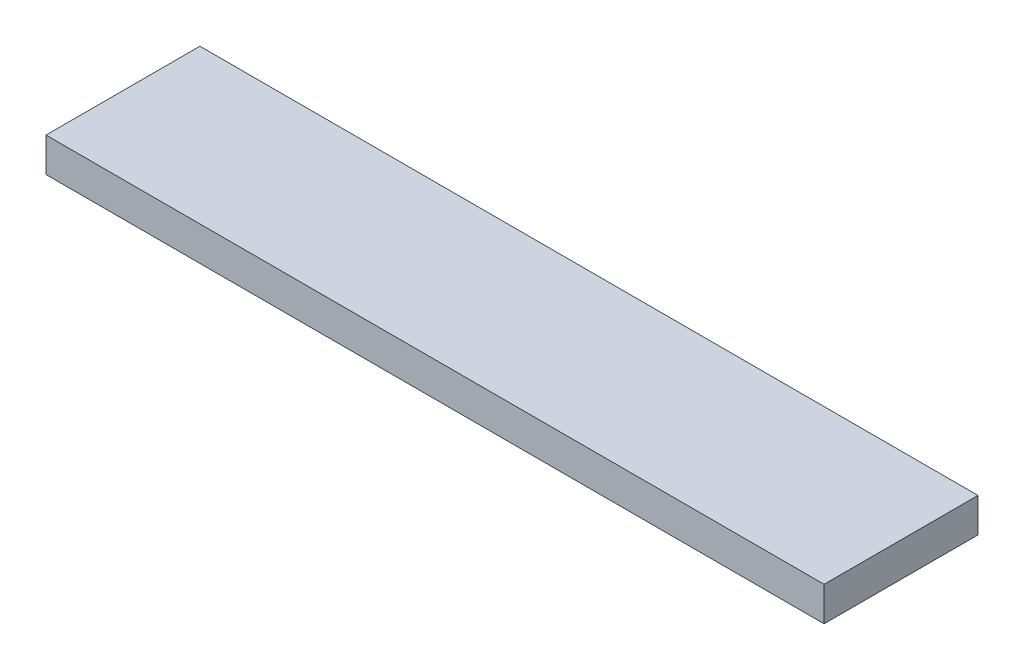
SolidWorks part; units mm, degrees
material "Polyurethane Foam Flexible"
ref_plane "Front Plane" through (0, 0, 0) normal (0, 0, 1) x (1, 0, 0)
ref_plane "Top Plane" through (0, 0, 0) normal (0, 1, 0) x (1, 0, 0)
ref_plane "Right Plane" through (0, 0, 0) normal (1, 0, 0) x (0, 0, -1)
sketch "Sketch1" plane through (0, 0, 0) normal (0, 1, 0) x (1, 0, 0)
  line L1 (0, 0) -> (182, 0)
  line L2 (0, 0) -> (0, 36)
  line L3 (0, 36) -> (182, 36)
  line L4 (182, 0) -> (182, 36)
  dimension "D1" = 36
  dimension "D2" = 182
extrude "Boss-Extrude1" add sketch "Sketch1" along normal blind 8
